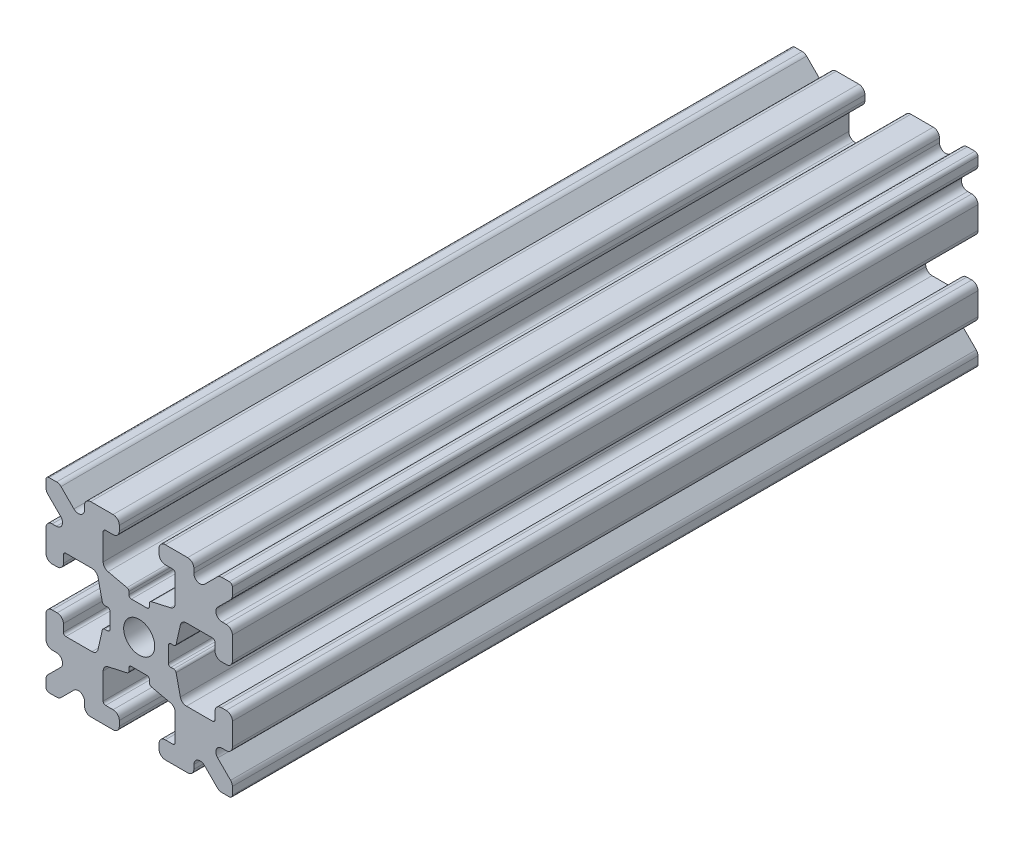
SolidWorks part; units mm, degrees
ref_plane "Front Plane" through (0, 0, 0) normal (0, 0, 1) x (1, 0, 0)
ref_plane "Top Plane" through (0, 0, 0) normal (0, 1, 0) x (1, 0, 0)
ref_plane "Right Plane" through (0, 0, 0) normal (1, 0, 0) x (0, 0, -1)
sketch "Sketch1" plane through (0, 0, 0) normal (0, 0, 1) x (1, 0, 0)
  line L1 (-7.5, -7.5) -> (7.5, -7.5)
  line L2 (-7.5, -7.5) -> (-7.5, 7.5)
  line L3 (-7.5, 7.5) -> (7.5, 7.5)
  line L4 (7.5, -7.5) -> (7.5, 7.5)
  line L5 (-7.5, -7.5) -> (7.5, 7.5) construction
  line L6 (-7.5, 7.5) -> (7.5, -7.5) construction
  circle A0 centre (0, 0) radius 1.25
  point P0 (0, 0)
  dimension "D2" = 2.5
  dimension "D1" = 15
extrude "Boss-Extrude1" add sketch "Sketch1" along normal mid plane 60
fillet "Fillet1" radius 0.25 4 edges at (7.5, -7.5, 0) (-7.5, -7.5, 0) (7.5, 7.5, 0) (-7.5, 7.5, 0)
sketch "Sketch2" plane through (0, 0, 30) normal (0, 0, 1) x (1, 0, 0)
  line L0 (-7.5, 7.25) -> (-7.5, -7.25) construction
  line L1 (-7.5, 1.6) -> (-6.1, 1.6)
  line L2 (-7.5, 1.6) -> (-7.5, -1.6)
  line L3 (-7.5, -1.6) -> (-6.1, -1.6)
  line L4 (-6.1, 1.6) -> (-6.1, 2.9)
  line L5 (0, 0) -> (-12.1036, 0) construction
  line L6 (-6.1, -2.9) -> (-3.4, -2.9)
  line L7 (0, 0) -> (-7.25, 7.25) construction
  line L8 (-6.1, 2.9) -> (-3.4, 2.9)
  line L9 (-3.4, -2.9) -> (-3.4, 2.9)
  line L10 (55, 0) -> (-55, 0) construction
  line L11 (-6.1, -2.9) -> (-6.1, -1.6)
  line L12 (2.9, 6.1) -> (1.6, 6.1)
  line L13 (2.9, 3.4) -> (-2.9, 3.4)
  line L14 (-2.9, 6.1) -> (-2.9, 3.4)
  line L15 (2.9, 6.1) -> (2.9, 3.4)
  line L16 (-1.6, 6.1) -> (-2.9, 6.1)
  line L17 (1.6, 7.5) -> (1.6, 6.1)
  line L18 (-1.6, 7.5) -> (1.6, 7.5)
  line L19 (-1.6, 7.5) -> (-1.6, 6.1)
  line L20 (-1.6, -7.5) -> (-1.6, -6.1)
  line L21 (-1.6, -7.5) -> (1.6, -7.5)
  line L22 (1.6, -7.5) -> (1.6, -6.1)
  line L23 (-1.6, -6.1) -> (-2.9, -6.1)
  line L24 (2.9, -6.1) -> (2.9, -3.4)
  line L25 (-2.9, -6.1) -> (-2.9, -3.4)
  line L26 (2.9, -3.4) -> (-2.9, -3.4)
  line L27 (2.9, -6.1) -> (1.6, -6.1)
  line L28 (6.1, -2.9) -> (6.1, -1.6)
  line L29 (3.4, -2.9) -> (3.4, 2.9)
  line L30 (6.1, 2.9) -> (3.4, 2.9)
  line L31 (6.1, -2.9) -> (3.4, -2.9)
  line L32 (6.1, 1.6) -> (6.1, 2.9)
  line L33 (7.5, -1.6) -> (6.1, -1.6)
  line L34 (7.5, 1.6) -> (7.5, -1.6)
  line L35 (7.5, 1.6) -> (6.1, 1.6)
  dimension "D1" = 3.2
  dimension "D2" = 5.8
  dimension "D3" = 1.4
  dimension "D4" = 2.7
extrude "Cut-Extrude1" cut sketch "Sketch2" against normal through all
sketch "Sketch4" plane through (0, 0, 30) normal (0, 0, 1) x (1, 0, 0)
  line L0 (-3.4, 2.9) -> (-2.75, 0)
  line L1 (55, 0) -> (-55, 0) construction
  line L2 (-2.75, 0) -> (-3.4, -2.9)
  line L3 (-3.4, -2.9) -> (-3.4, 2.9) construction
  line L4 (-3.4, 2.9) -> (-3.4, -2.9)
  line L5 (-2.9, 3.4) -> (0, 2.75)
  line L6 (0, 2.75) -> (2.9, 3.4)
  line L7 (2.9, 3.4) -> (-2.9, 3.4)
  line L8 (3.4, 2.9) -> (2.75, 0)
  line L9 (2.75, 0) -> (3.4, -2.9)
  line L10 (3.4, -2.9) -> (3.4, 2.9)
  line L11 (-2.9, -3.4) -> (0, -2.75)
  line L12 (0, -2.75) -> (2.9, -3.4)
  line L13 (2.9, -3.4) -> (-2.9, -3.4)
  circle A2 centre (0, 0) radius 2.75
  circle A3 centre (0, 0) radius 2.75 construction
  dimension "D1" = 1.5
extrude "Cut-Extrude3" cut sketch "Sketch4" against normal through all
fillet "Fillet3" radius 0.5 16 edges at (-6.1, -1.6, 0) (-7.5, -1.6, 0) (-6.1, 1.6, 0) (-7.5, 1.6, 0) (-1.6, -7.5, 0) (-1.6, -6.1, 0) (1.6, -7.5, 0) (1.6, -6.1, 0) (6.1, -1.6, 0) (7.5, -1.6, 0) (7.5, 1.6, 0) (6.1, 1.6, 0) (1.6, 7.5, 0) (1.6, 6.1, 0) (-1.6, 7.5, 0) (-1.6, 6.1, 0)
fillet "Fillet4" radius 0.5 8 edges at (-3.4, 2.9, 0) (-3.4, -2.9, 0) (2.9, -3.4, 0) (-2.9, -3.4, 0) (3.4, -2.9, 0) (3.4, 2.9, 0) (-2.9, 3.4, 0) (2.9, 3.4, 0)
fillet "Fillet5" radius 3 4 edges at (0, -2.75, 0) (2.75, 0, 0) (-2.75, 0, 0) (0, 2.75, 0)
fillet "Fillet6" radius 0.2 8 edges at (-2.9, -6.1, 0) (2.9, -6.1, 0) (6.1, -2.9, 0) (6.1, 2.9, 0) (2.9, 6.1, 0) (-2.9, 6.1, 0) (-6.1, -2.9, 0) (-6.1, 2.9, 0)
sketch "Sketch5" plane through (0, 0, 30) normal (0, 0, 1) x (1, 0, 0)
  line L0 (0, 0) -> (-7.25, 7.25) construction
  line L1 (-7.5, 6.4393) -> (-5.4607, 4.4)
  line L2 (-6.4393, 7.5) -> (-4.4, 5.4607)
  line L3 (-7.5, 4.4) -> (-5.4607, 4.4)
  line L4 (-3.8003, 2.9) -> (-5.9, 2.9) construction
  line L5 (0, 0) -> (-12.1819, 0) construction
  line L6 (-4.4, 7.5) -> (-4.4, 5.4607)
  line L7 (-2.9, 5.9) -> (-2.9, 3.8003) construction
  line L8 (-7.5, 6.4393) -> (-7.5, 4.4)
  line L9 (-7.5, 7.25) -> (-7.5, 2.1) construction
  line L10 (2.1, -7.5) -> (7.25, -7.5) construction
  line L11 (7.5, -7.25) -> (7.5, -2.1) construction
  line L12 (7.25, 7.5) -> (2.1, 7.5) construction
  line L13 (-2.1, 7.5) -> (-7.25, 7.5) construction
  line L14 (-4.4, 7.5) -> (-6.4393, 7.5)
  line L16 (55, 0) -> (-55, 0) construction
  line L17 (0, 0) -> (0, 10.993) construction
  line L18 (0, -54.6431) -> (0, 54.6431) construction
  line L20 (4.4, 7.5) -> (6.4393, 7.5)
  line L22 (7.5, 6.4393) -> (7.5, 4.4)
  line L23 (4.4, 7.5) -> (4.4, 5.4607)
  line L24 (7.5, 4.4) -> (5.4607, 4.4)
  line L25 (6.4393, 7.5) -> (4.4, 5.4607)
  line L26 (7.5, 6.4393) -> (5.4607, 4.4)
  line L27 (7.5, -6.4393) -> (5.4607, -4.4)
  line L28 (6.4393, -7.5) -> (4.4, -5.4607)
  line L29 (7.5, -4.4) -> (5.4607, -4.4)
  line L30 (4.4, -7.5) -> (4.4, -5.4607)
  line L31 (7.5, -6.4393) -> (7.5, -4.4)
  line L33 (4.4, -7.5) -> (6.4393, -7.5)
  line L36 (-4.4, -7.5) -> (-6.4393, -7.5)
  line L38 (-7.5, -6.4393) -> (-7.5, -4.4)
  line L39 (-4.4, -7.5) -> (-4.4, -5.4607)
  line L40 (-7.5, -4.4) -> (-5.4607, -4.4)
  line L41 (-6.4393, -7.5) -> (-4.4, -5.4607)
  line L42 (-7.5, -6.4393) -> (-5.4607, -4.4)
  dimension "D1" = 1.5
  dimension "D2" = 1.5
  dimension "D3" = 1.5
extrude "Cut-Extrude4" cut sketch "Sketch5" against normal through all
fillet "Fillet8" radius 0.5 24 edges at (-5.4607, 4.4, 0) (-7.5, 4.4, 0) (-5.4607, -4.4, 0) (-7.5, -4.4, 0) (-4.4, -7.5, 0) (-4.4, -5.4607, 0) (4.4, -7.5, 0) (4.4, -5.4607, 0) (5.4607, -4.4, 0) (7.5, -4.4, 0) (7.5, 4.4, 0) (5.4607, 4.4, 0) (4.4, 5.4607, 0) (4.4, 7.5, 0) (-4.4, 5.4607, 0) (-4.4, 7.5, 0) (-6.4393, 7.5, 0) (-7.5, 6.4393, 0) (6.4393, 7.5, 0) (7.5, 6.4393, 0) (6.4393, -7.5, 0) (7.5, -6.4393, 0) (-6.4393, -7.5, 0) (-7.5, -6.4393, 0)
sketch "Sketch6" plane through (0, 0, 30) normal (0, 0, 1) x (1, 0, 0)
  line L0 (0, 0) -> (0, 11.013) construction
  line L1 (0.6561, 2.8971) -> (2.1235, 2.8971) construction
  line L2 (0, -54.6431) -> (0, 54.6431) construction
  line L3 (0, 0) -> (7.25, 7.25) construction
  line L4 (7.5, 0.8255) -> (7.5, -0.8255)
  line L5 (2.3471, 0.8255) -> (7.5, 0.8255)
  line L6 (0, 0) -> (12.4016, 0) construction
  line L7 (0.8255, -7.5) -> (-0.8255, -7.5)
  line L8 (2.3471, -0.8255) -> (2.3471, 0.8255)
  line L9 (0.8255, -2.3471) -> (0.8255, -7.5)
  line L10 (7.5, -0.8255) -> (2.3471, -0.8255)
  line L11 (-7.5, -0.8255) -> (-2.3471, -0.8255)
  line L12 (-2.3471, -0.8255) -> (-2.3471, 0.8255)
  line L13 (-0.8255, -2.3471) -> (0.8255, -2.3471)
  line L14 (-0.8255, 7.5) -> (-0.8255, 2.3471)
  line L15 (-0.8255, 2.3471) -> (0.8255, 2.3471)
  line L16 (-0.8255, -7.5) -> (-0.8255, -2.3471)
  line L17 (0.8255, 2.3471) -> (0.8255, 7.5)
  line L18 (0.8255, 7.5) -> (-0.8255, 7.5)
  line L19 (3.9, 7.5) -> (2.1, 7.5) construction
  line L20 (-2.3471, 0.8255) -> (-7.5, 0.8255)
  line L21 (-7.5, 0.8255) -> (-7.5, -0.8255)
  point P5 (0, -2.5973)
  point P7 (0, 2.5973)
  dimension "D3" = 0.55
  dimension "D1" = 1.651
extrude "Cut-Extrude5" cut sketch "Sketch6" against normal through all
fillet "Fillet10" radius 0.2 16 edges at (-2.935, 0.8255, 0) (-2.935, -0.8255, 0) (2.935, -0.8255, 0) (2.935, 0.8255, 0) (0.8255, 2.935, 0) (-0.8255, 2.935, 0) (-2.3471, 0.8255, 0) (-2.3471, -0.8255, 0) (0.8255, 2.3471, 0) (-0.8255, 2.3471, 0) (2.3471, 0.8255, 0) (2.3471, -0.8255, 0) (0.8255, -2.935, 0) (0.8255, -2.3471, 0) (-0.8255, -2.3471, 0) (-0.8255, -2.935, 0)
